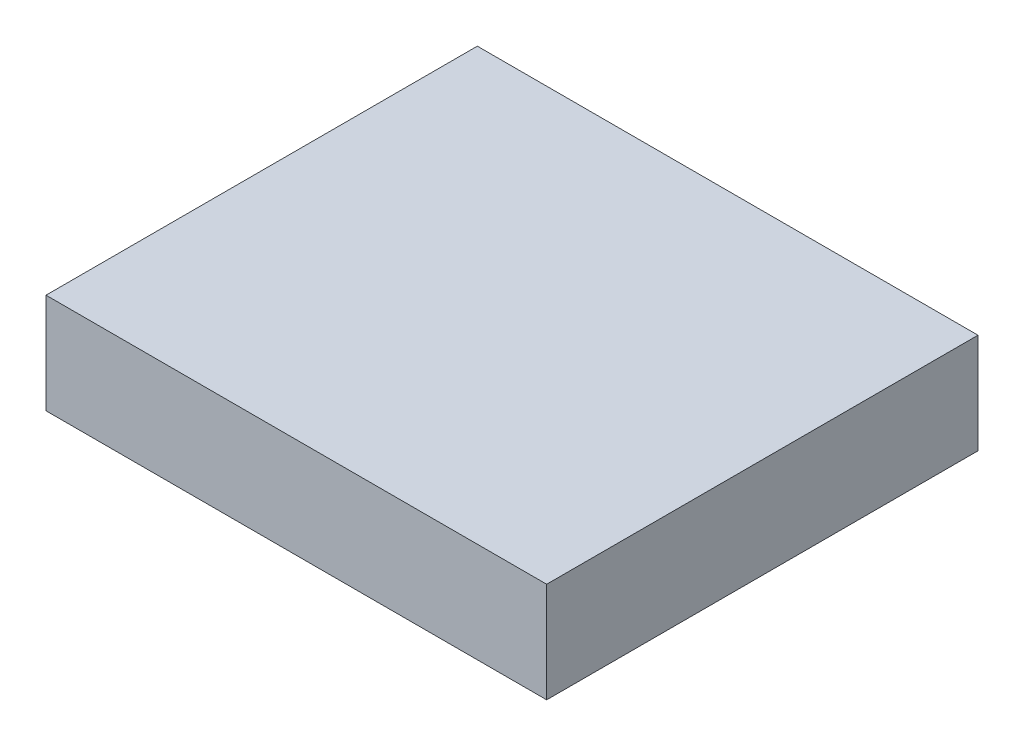
SolidWorks part; units mm, degrees
ref_plane "Front Plane" through (0, 0, 0) normal (0, 0, 1) x (1, 0, 0)
ref_plane "Top Plane" through (0, 0, 0) normal (0, 1, 0) x (1, 0, 0)
ref_plane "Right Plane" through (0, 0, 0) normal (1, 0, 0) x (0, 0, -1)
sketch "Sketch1" plane through (0, 0, 0) normal (0, 1, 0) x (1, 0, 0)
  line L1 (0, 0) -> (65, 0)
  line L2 (0, 0) -> (0, 56)
  line L3 (0, 56) -> (65, 56)
  line L4 (65, 0) -> (65, 56)
extrude "Boss-Extrude1" add sketch "Sketch1" along normal blind 13
